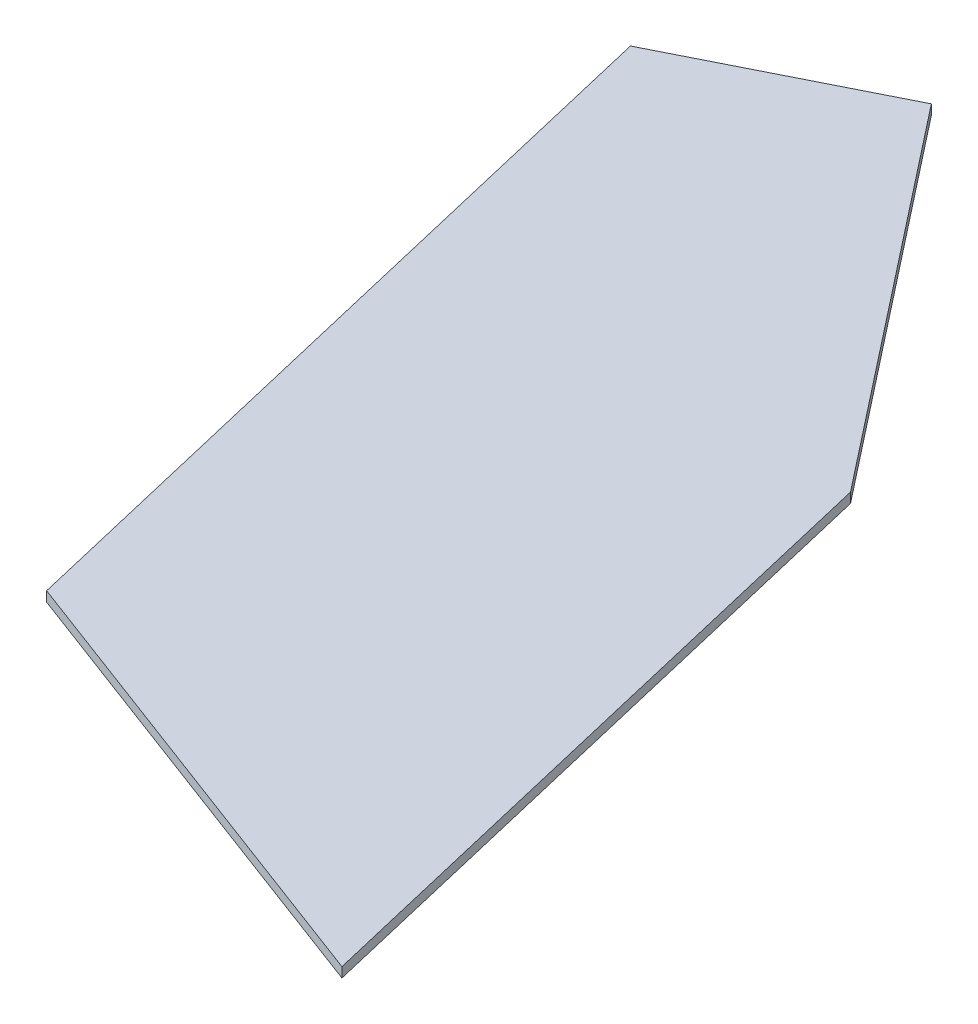
SolidWorks part; units mm, degrees
ref_plane "Plan de face" through (0, 0, 0) normal (0, 0, 1) x (1, 0, 0)
ref_plane "Plan de dessus" through (0, 0, 0) normal (0, 1, 0) x (1, 0, 0)
ref_plane "Plan de droite" through (0, 0, 0) normal (1, 0, 0) x (0, 0, -1)
sketch "Esquisse1" plane through (0, 0, 0) normal (0, 1, 0) x (1, 0, 0)
  line L0 (-36.5071, 154.9964) -> (0, 0)
  line L1 (0, 0) -> (96.0241, -36.0939)
  line L2 (96.0241, -36.0939) -> (64.2218, 98.9277)
  line L3 (64.2218, 98.9277) -> (4.195, 175.3632)
  line L4 (4.195, 175.3632) -> (-36.5071, 154.9964)
  point P5 (0, 0)
extrude "Boss.-Extru.1" add sketch "Esquisse1" along normal blind 2
